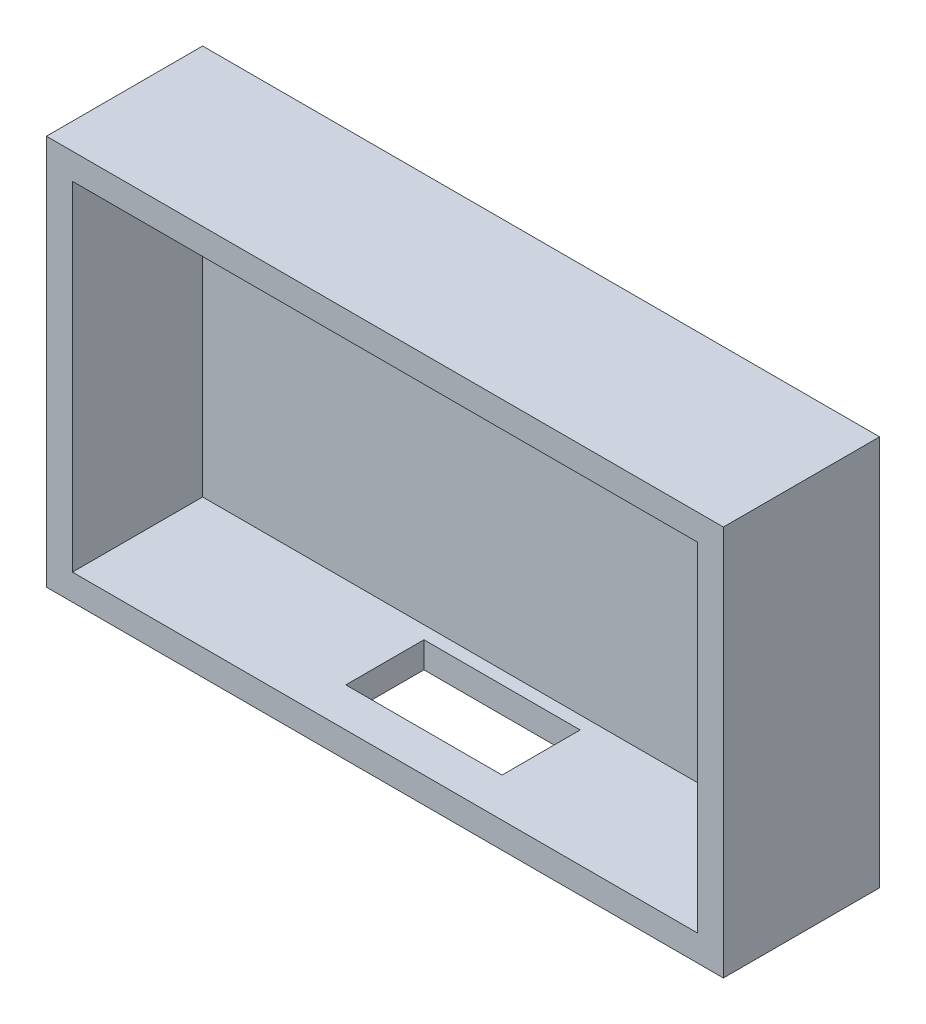
SolidWorks part; units mm, degrees
ref_plane "Front Plane" through (0, 0, 0) normal (0, 0, 1) x (1, 0, 0)
ref_plane "Top Plane" through (0, 0, 0) normal (0, 1, 0) x (1, 0, 0)
ref_plane "Right Plane" through (0, 0, 0) normal (1, 0, 0) x (0, 0, -1)
sketch "Sketch1" plane through (0, 0, 0) normal (0, 1, 0) x (1, 0, 0)
  line L1 (0, 0) -> (130, 0)
  line L2 (0, 0) -> (0, 30)
  line L3 (0, 30) -> (130, 30)
  line L4 (130, 0) -> (130, 30)
  dimension "D1" = 130
  dimension "D2" = 30
extrude "Boss-Extrude1" add sketch "Sketch1" along normal blind 75
shell "Shell1" thickness 5
sketch "Sketch2" plane through (0, 0, 0) normal (0, -1, 0) x (1, 0, 0)
  line L0 (0, -30) -> (130, 0) construction
  line L1 (50, -22.5) -> (80, -22.5)
  line L2 (50, -22.5) -> (50, -7.5)
  line L3 (50, -7.5) -> (80, -7.5)
  line L4 (80, -22.5) -> (80, -7.5)
  line L5 (50, -22.5) -> (80, -7.5) construction
  line L6 (50, -7.5) -> (80, -22.5) construction
  point P0 (65, -15)
  point P9 (0, 0)
  dimension "D1" = 30
  dimension "D2" = 15
extrude "Cut-Extrude1" cut sketch "Sketch2" against normal up to next
